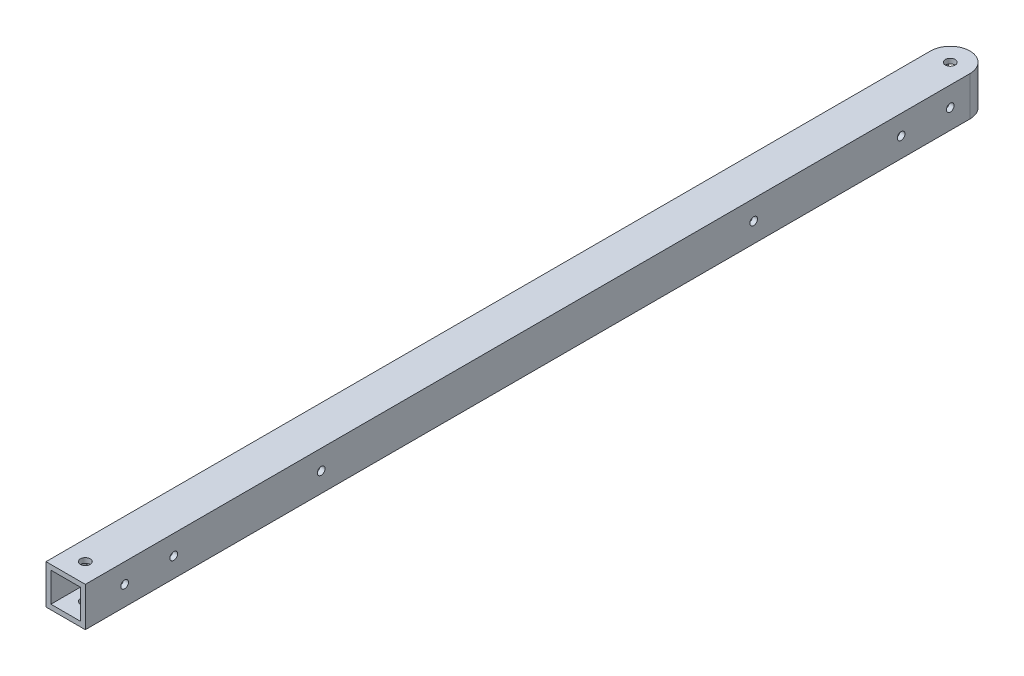
SolidWorks part; units mm, degrees
ref_plane "Front Plane" through (0, 0, 0) normal (0, 0, 1) x (1, 0, 0)
ref_plane "Top Plane" through (0, 0, 0) normal (0, 1, 0) x (1, 0, 0)
ref_plane "Right Plane" through (0, 0, 0) normal (1, 0, 0) x (0, 0, -1)
sketch "Sketch1" plane through (0, 0, 0) normal (0, 0, 1) x (1, 0, 0)
  line L1 (-12.7, -12.7) -> (12.7, -12.7)
  line L2 (-12.7, -12.7) -> (-12.7, 12.7)
  line L3 (-12.7, 12.7) -> (12.7, 12.7)
  line L4 (12.7, -12.7) -> (12.7, 12.7)
  line L5 (-12.7, -12.7) -> (12.7, 12.7) construction
  line L6 (-12.7, 12.7) -> (12.7, -12.7) construction
  point P0 (0, 0)
  dimension "D1" = 25.4
  dimension "D2" = 25.4
extrude "Extrude-Thin1" add sketch "Sketch1" along normal mid plane 584.2 thin thin type one direction reverse wall 3.175
sketch "Sketch3" plane through (0, 12.7, 0) normal (0, 1, 0) x (1, 0, 0)
  line L0 (12.7, 292.1) -> (-12.7, 292.1) construction
  line L1 (-13.97, 0) -> (13.97, 0) construction
  circle A0 centre (0, 279.4) radius 3.175
  circle A1 centre (0, -279.4) radius 3.175
  dimension "D1" = 6.35
  dimension "D2" = 12.7
sketch "Sketch4" plane through (-12.7, 0, 0) normal (-1, 0, 0) x (0, 0, 1)
  line L1 (292.1, 12.7) -> (292.1, -12.7) construction
  line L3 (292.1, 0) -> (266.7, 0) construction
  line L5 (266.7, 0) -> (139.7, 0) construction
  circle A0 centre (266.7, 0) radius 2.4892
  circle A5 centre (139.7, 0) radius 2.4892
  circle A6 centre (234.95, 0) radius 2.4892
  dimension "D1" = 4.9784
  dimension "D2" = 127
  dimension "D3" = 25.4
extrude "Cut-Extrude1" cut sketch "Sketch4" against normal through all
ref_plane "Plane1" through (0, 0, 0) normal (0, 0, -1) x (-1, 0, 0)
mirror "Mirror1" about plane through (0, 0, 0) normal (0, 0, -1) of "Cut-Extrude1"
sketch "Sketch5" plane through (0, -12.7, 0) normal (0, -1, 0) x (1, 0, 0)
  line L0 (-12.7, 292.1) -> (-12.7, -292.1) construction
  line L1 (12.7, 292.1) -> (12.7, -292.1) construction
  line L2 (-12.7, -292.1) -> (12.7, -292.1) construction
  line L4 (12.7, -279.4) -> (-12.7, -279.4)
  line L5 (12.7, -279.4) -> (12.7, -298.45)
  line L6 (12.7, -298.45) -> (-12.7, -298.45)
  line L7 (-12.7, -279.4) -> (-12.7, -298.45)
  arc A0 (-12.7, -279.4) -> (12.7, -279.4) centre (0, -279.4) ccw
  point P8 (0, -292.1)
  line M5 (-12.7, -292.1) -> (12.7, -292.1)
  line M6 (12.7, -292.1) -> (12.7, 292.1)
  line M8 (-12.7, 292.1) -> (-12.7, -292.1)
  dimension "D1" = 6.35
extrude "Cut-Extrude2" cut sketch "Sketch5" against normal through all contours L7 L6 L5 M5 | A0 M8 M5 | A0 M5 M6
extrude "Cut-Extrude3" cut sketch "Sketch3" against normal through all
